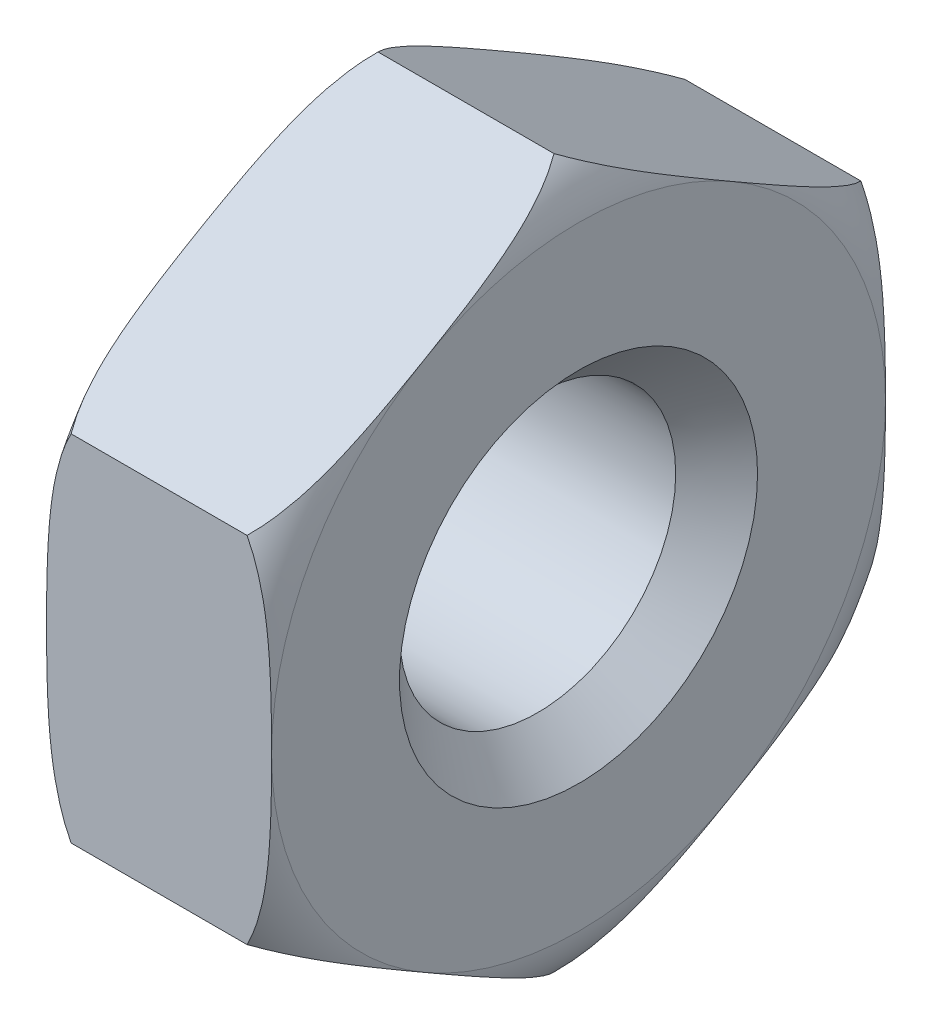
SolidWorks part; units mm, degrees
ref_plane "Plan de face" through (0, 0, 0) normal (0, 0, 1) x (1, 0, 0)
ref_plane "Plan de dessus" through (0, 0, 0) normal (0, 1, 0) x (1, 0, 0)
ref_plane "Plan de droite" through (0, 0, 0) normal (1, 0, 0) x (0, 0, -1)
sketch "Esquisse1" plane through (0, 0, 0) normal (1, 0, 0) x (0, 0, -1)
  line L1 (0, 8.6603) -> (-7.5, 4.3301)
  line L2 (-7.5, 4.3301) -> (-7.5, -4.3301)
  line L3 (-7.5, -4.3301) -> (0, -8.6603)
  line L4 (0, -8.6603) -> (7.5, -4.3301)
  line L5 (7.5, -4.3301) -> (7.5, 4.3301)
  line L6 (7.5, 4.3301) -> (0, 8.6603)
  circle A0 centre (0, 0) radius 7.5 construction
  dimension "D1" = 15
extrude "Extrusion1" add sketch "Esquisse1" along normal blind 7
sketch "Esquisse2" plane through (0, 0, 0) normal (0, 0, 1) x (1, 0, 0)
  line L0 (0, 4.3301) -> (0, -4.3301) construction
  line L2 (1.5, 6.75) -> (1.5, 8.6603)
  line L3 (7, 8.6603) -> (0, 8.6603) construction
  line L4 (1.5, 8.6603) -> (0, 8.6603)
  line L5 (0, 8.6603) -> (0, 5.25)
  line L6 (-3.0404, 0) -> (7.5495, 0) construction
  arc A0 (0, 5.25) -> (1.5, 6.75) centre (0, 6.75) ccw
  dimension "D1" = 13.5
  dimension "D2" = 1.5
revolve "Enlèvement de matière-Révolution1" cut sketch "Esquisse2" angle 360 about L6
sketch "Esquisse3" plane through (0, 0, 0) normal (-1, 0, 0) x (0, 0, 1)
  circle A0 centre (0, 0) radius 3.375
  dimension "D1" = 6.75
extrude "Enlèv. mat.-Extru.1" cut sketch "Esquisse3" against normal through all
chamfer "Chanfrein1" distance 1 angle 45 2 edges at (7, 0, 3.375) (0, 0, 3.375)
sketch "Esquisse4" plane through (0, 0, 0) normal (0, 0, 1) x (1, 0, 0)
  line L0 (4.25, 9.1813) -> (4.25, -9.5207) construction
  line L1 (7, 8.6603) -> (7, 4.3301) construction
  line L2 (1.5, 4.3301) -> (1.5, 8.6603) construction
  line L3 (1.5, 8.6603) -> (2.1, 8.6603)
  line L5 (1.5, 8.6603) -> (1.5, 7.5)
  line L6 (7, 8.6603) -> (1.5, 8.6603) construction
  line L7 (0, 0) -> (10.1699, 0) construction
  line L8 (7, 8.6603) -> (7, 7.5)
  line L9 (7, 8.6603) -> (6.4, 8.6603)
  arc A0 (2.1, 8.6603) -> (1.5, 7.5) centre (3.4791, 7.2118) ccw
  arc A1 (6.4, 8.6603) -> (7, 7.5) centre (5.0209, 7.2118) cw
  dimension "D1" = 2
  dimension "D2" = 15
  dimension "D3" = 0.6
revolve "Enlèvement de matière-Révolution2" cut sketch "Esquisse4" angle 360 about L7
